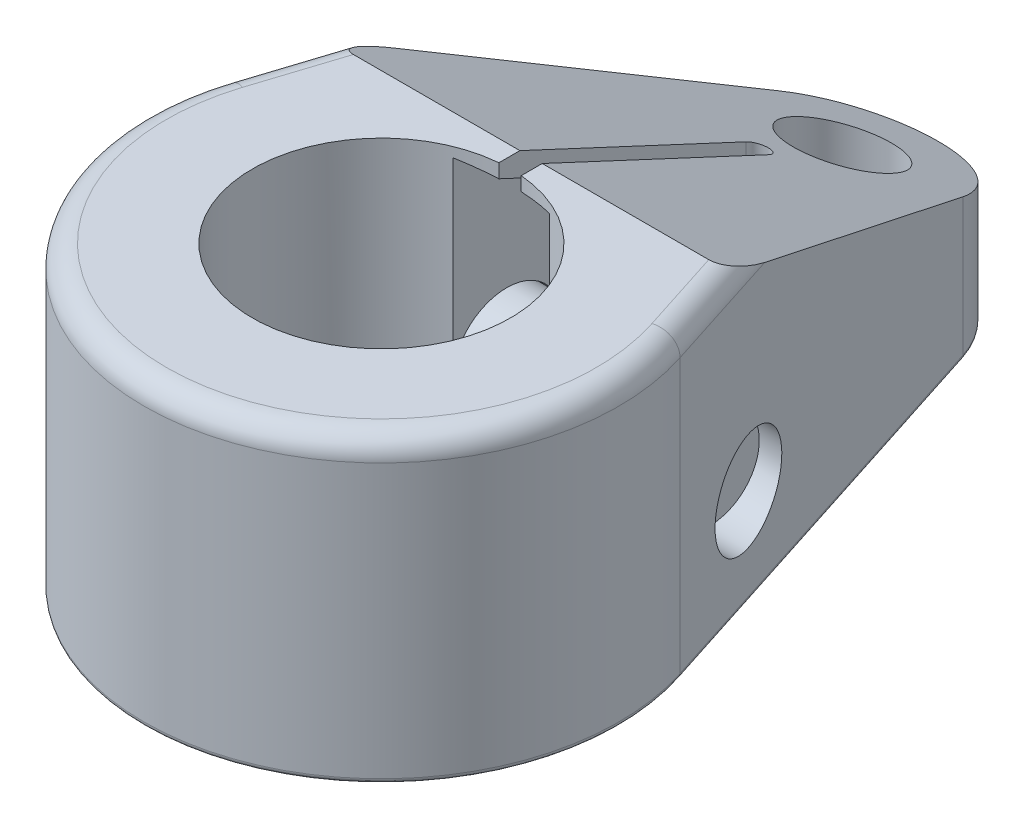
SolidWorks part; units mm, degrees
material "Alloy Steel"
ref_plane "Front Plane" through (0, 0, 0) normal (0, 0, 1) x (1, 0, 0)
ref_plane "Top Plane" through (0, 0, 0) normal (0, 1, 0) x (1, 0, 0)
ref_plane "Right Plane" through (0, 0, 0) normal (1, 0, 0) x (0, 0, -1)
sketch "Sketch1" plane through (0, 0, 0) normal (0, 1, 0) x (1, 0, 0)
  line L0 (-13.5403, 72.3528) -> (-33.3671, 10.7369)
  line L1 (0, 67.9958) -> (0, 0) construction
  line L2 (13.5403, 72.3528) -> (33.3671, 10.7369)
  circle A0 centre (0, 0) radius 19.0691
  arc A1 (-33.3671, 10.7369) -> (33.3671, 10.7369) centre (0, 0) ccw
  arc A2 (13.5403, 72.3528) -> (-13.5403, 72.3528) centre (0, 67.9958) ccw
  dimension "D1" = 38.1381
  dimension "D2" = 35.052
  dimension "D3" = 14.224
  dimension "D4" = 117.2718
extrude "Extrude1" add sketch "Sketch1" along normal blind 44.45
sketch "Sketch2" plane through (0, 0, 0) normal (1, 0, 0) x (0, 0, -1)
  line L0 (22.098, 44.45) -> (82.2198, 16.4147)
  line L1 (72.3528, 44.45) -> (10.7369, 44.45) construction
  line L2 (82.2198, 0) -> (82.2198, 44.45) construction
  line L3 (82.2198, 16.4147) -> (82.2198, 44.45)
  line L4 (82.2198, 44.45) -> (22.098, 44.45)
  line L5 (-35.052, 44.45) -> (-35.052, 0) construction
  dimension "D1" = 57.15
  dimension "D2" = 25
extrude "Cut-Extrude1" cut sketch "Sketch2" against normal through all and the other way through all
sketch "Sketch3" plane through (0, 0, 0) normal (0, -1, 0) x (1, 0, 0)
  line L0 (0, 0) -> (0, -101.5721) construction
  line L1 (-7.1374, -13.4874) -> (-7.1374, -50.0126)
  line L2 (7.1374, -13.4874) -> (7.1374, -50.0126)
  arc A0 (-7.1374, -13.4874) -> (7.1374, -13.4874) centre (0, -13.4874) cw
  arc A1 (-7.1374, -50.0126) -> (7.1374, -50.0126) centre (0, -50.0126) ccw
  dimension "D1" = 6.35
  dimension "D2" = 57.15
  dimension "D3" = 14.2748
extrude "Cut-Extrude2" cut sketch "Sketch3" against normal offset from surface (44.962 mm away) 3.175
sketch "Sketch4" plane through (0, 0, 0) normal (0, -1, 0) x (1, 0, 0)
  line L0 (0, 0) -> (0, -69.4753) construction
  line L1 (-1.651, 0) -> (-1.651, -55.499)
  line L2 (1.651, 0) -> (1.651, -55.499)
  line L3 (-1.651, 0) -> (1.651, 0)
  arc A0 (-1.651, -55.499) -> (1.651, -55.499) centre (0, -55.499) ccw
  arc A1 (-7.1374, -50.0126) -> (7.1374, -50.0126) centre (0, -50.0126) ccw construction
  dimension "D1" = 3.302
extrude "Cut-Extrude3" cut sketch "Sketch4" against normal through all
ref_plane "Plane1" through (0, 0, -25.629) normal (0, 0, 1) x (1, 0, 0)
sketch "Sketch5" plane through (0, 0, -25.629) normal (0, 0, 1) x (1, 0, 0)
  line L0 (-30.1073, 14.2748) -> (29.8831, 14.2748) construction
  line L1 (-35.052, 31.7373) -> (-25.4762, 31.7373)
  line L2 (-25.4762, 31.7373) -> (-25.4762, 22.4028)
  line L3 (-25.4762, 22.4028) -> (7.1374, 22.4028)
  line L4 (7.1374, 22.4028) -> (7.1374, 21.5392)
  line L5 (35.052, 14.2748) -> (-35.052, 14.2748)
  line L6 (-35.052, 14.2748) -> (-35.052, 31.7373)
  line L7 (-35.052, 0) -> (35.052, 0) construction
  line L9 (-35.052, 44.45) -> (-35.052, 0) construction
  line L10 (7.1374, 21.5392) -> (35.052, 21.5392)
  line L11 (35.052, 21.5392) -> (35.052, 14.2748)
  line L12 (35.052, 0) -> (35.052, 44.45) construction
  line L13 (7.1374, 0) -> (7.1374, 43.0056) construction
  dimension "D1" = 14.2748
  dimension "D2" = 16.256
  dimension "D3" = 34.925
  dimension "D4" = 9.5758
  dimension "D5" = 14.5288
revolve "Cut-Revolve1" cut sketch "Sketch5" angle 360 about L0
sketch "Sketch6" plane through (-25.4762, 0, 0) normal (-1, 0, 0) x (0, 0, 1)
  line L1 (-11.7709, 14.2748) -> (-18.6999, 26.2763)
  line L2 (-18.6999, 26.2763) -> (-32.5581, 26.2763)
  line L3 (-32.5581, 26.2763) -> (-39.4871, 14.2748)
  line L4 (-39.4871, 14.2748) -> (-32.5581, 2.2733)
  line L5 (-32.5581, 2.2733) -> (-18.6999, 2.2733)
  line L6 (-18.6999, 2.2733) -> (-11.7709, 14.2748)
  circle A0 centre (-25.629, 14.2748) radius 12.0015 construction
  dimension "D1" = 24.003
extrude "Extrude2" add sketch "Sketch6" along normal blind 10.0076
sketch "Sketch7" plane through (-25.4762, 0, 0) normal (-1, 0, 0) x (0, 0, 1)
  circle A0 centre (-25.629, 14.2748) radius 8.001
  dimension "D1" = 16.002
extrude "Extrude3" add sketch "Sketch7" against normal blind 48.387
sketch "Sketch8" plane through (0, 0, -25.629) normal (0, 0, 1) x (1, 0, 0)
  line L0 (-5.5513, 14.2748) -> (-39.7173, 14.2748) construction
  line L1 (7.1374, 14.2748) -> (-25.4762, 14.2748) construction
  line L2 (-21.5456, 14.2748) -> (-47.2308, 14.2748) construction
  line L3 (-35.4838, 2.2733) -> (-35.4838, -0.9017)
  line L4 (-35.4838, -0.9017) -> (-33.6507, -0.9017)
  line L5 (-33.6507, -0.9017) -> (-35.4838, 2.2733)
  dimension "D1" = 30
  dimension "D2" = 3.175
revolve "Cut-Revolve2" cut sketch "Sketch8" angle 360 about L0
sketch "Sketch9" plane through (0, 0, 0) normal (0, -1, 0) x (1, 0, 0)
  circle A0 centre (0, -68.072) radius 7.2644
  dimension "D1" = 14.5288
  dimension "D2" = 68.072
extrude "Cut-Extrude4" cut sketch "Sketch9" against normal through all
fillet "Fillet1" radius 3.302 3 edges at (-31.5392, 44.45, -16.4174) (31.5392, 44.45, -16.4174) (0, 44.45, 35.052)
fillet "Fillet2" radius 0.762 5 edges at (-32.5894, 0, -13.1538) (0, 0, 35.052) (23.4537, 0, -41.5448) (0, 0, -82.2198) (-19.5082, 0, -53.8061)
